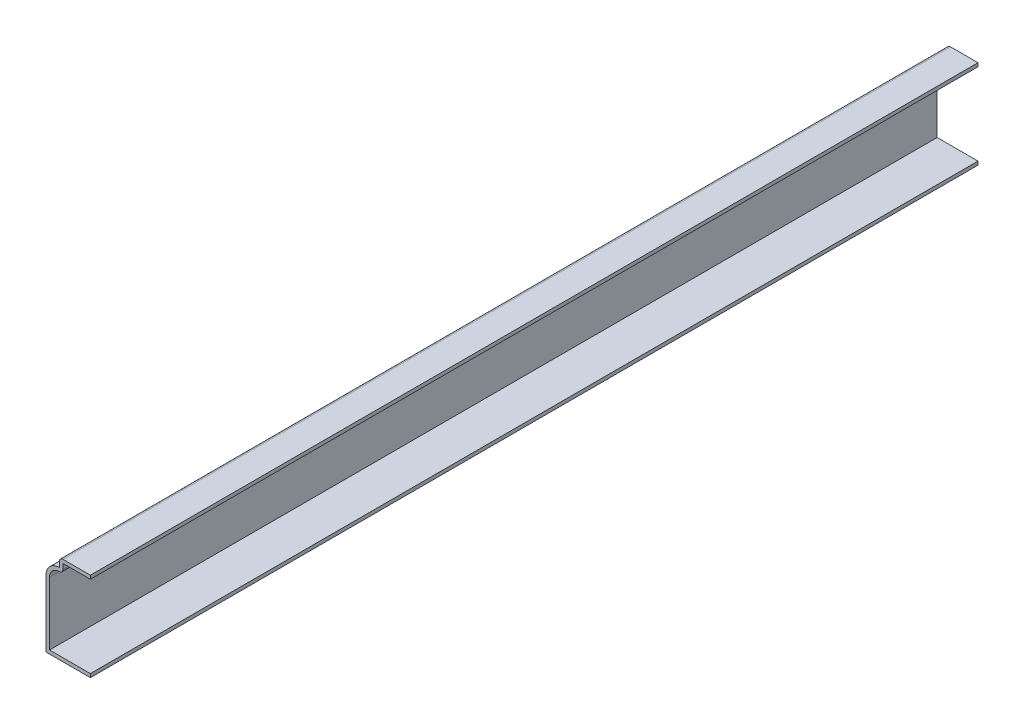
SolidWorks part; units mm, degrees
ref_plane "Front Plane" through (0, 0, 0) normal (0, 0, 1) x (1, 0, 0)
ref_plane "Top Plane" through (0, 0, 0) normal (0, 1, 0) x (1, 0, 0)
ref_plane "Right Plane" through (0, 0, 0) normal (1, 0, 0) x (0, 0, -1)
sketch "Sketch1" plane through (0, 0, 0) normal (0, 0, 1) x (1, 0, 0)
  line L0 (0, 0) -> (-15.875, 0)
  line L1 (-15.875, 0) -> (-15.875, 23.8125)
  line L2 (-11.1125, 28.575) -> (-11.1125, 31.75)
  line L3 (-11.1125, 31.75) -> (0, 31.75)
  arc A0 (-15.875, 23.8125) -> (-11.1125, 28.575) centre (-11.1125, 23.8125) cw
  point P6 (0, 0)
  point P9 (0, 0)
  dimension "D1" = 15.875
  dimension "D2" = 31.75
  dimension "D3" = 28.575
  dimension "D4" = 3.175
  dimension "D5" = 4.7625
  dimension "D6" = 11.1125
  dimension "D7" = 15.875
extrude "Extrude-Thin1" add sketch "Sketch1" against normal blind 317.5 thin
fillet "Fillet1" radius 1.27 2 edges at (-9.8425, 27.0659, -158.75) (-11.1125, 31.75, -158.75)
